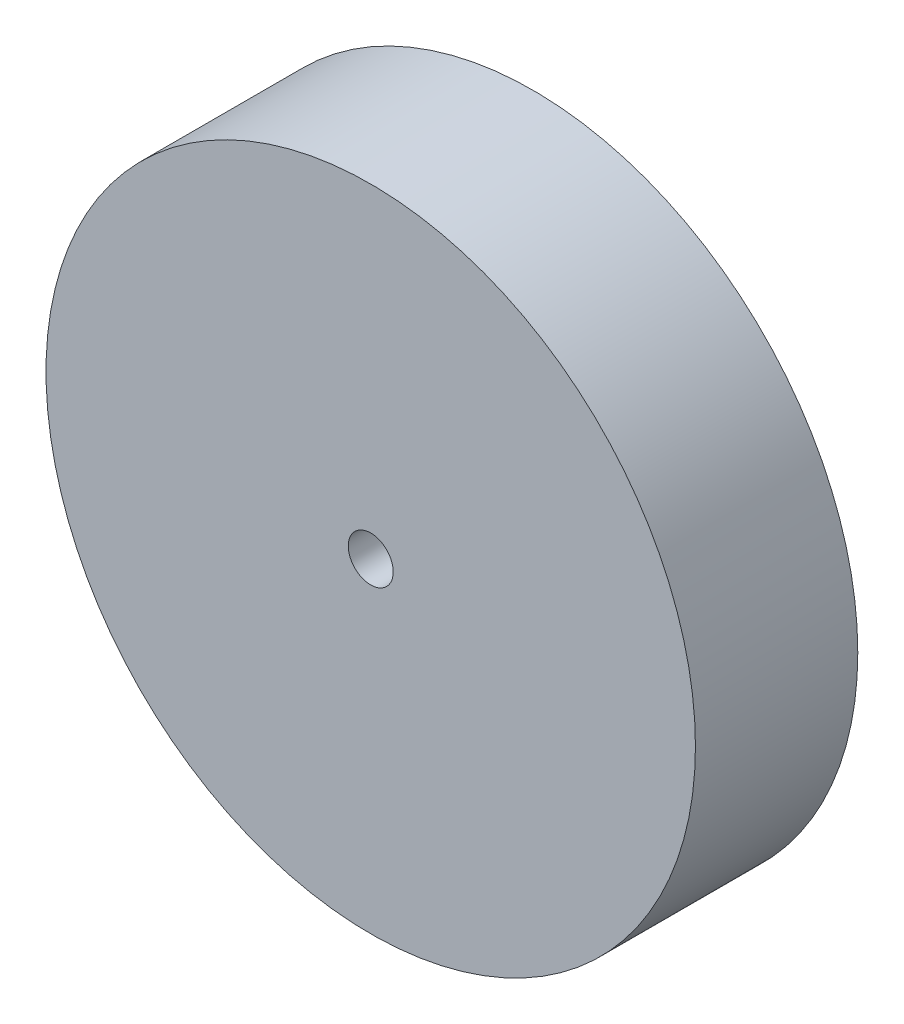
SolidWorks part; units mm, degrees
ref_plane "Front Plane" through (0, 0, 0) normal (0, 0, 1) x (1, 0, 0)
ref_plane "Top Plane" through (0, 0, 0) normal (0, 1, 0) x (1, 0, 0)
ref_plane "Right Plane" through (0, 0, 0) normal (1, 0, 0) x (0, 0, -1)
sketch "Sketch1" plane through (0, 0, 0) normal (0, 0, 1) x (1, 0, 0)
  circle A0 centre (0, 0) radius 10
  dimension "D1" = 20
extrude "Boss-Extrude1" add sketch "Sketch1" along normal blind 5
sketch "Sketch2" plane through (0, 0, 5) normal (0, 0, 1) x (1, 0, 0)
  circle A0 centre (0, 0) radius 0.6929
  dimension "D1" = 1.3857
extrude "Cut-Extrude1" cut sketch "Sketch2" against normal blind 10
